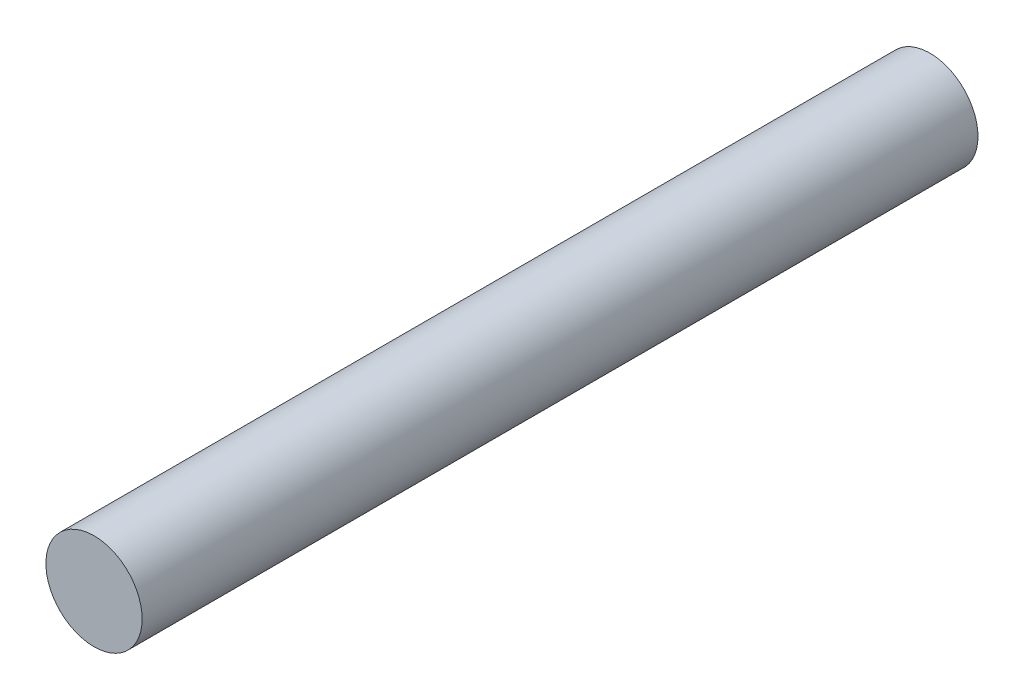
SolidWorks part; units mm, degrees
ref_plane "Front Plane" through (0, 0, 0) normal (0, 0, 1) x (1, 0, 0)
ref_plane "Top Plane" through (0, 0, 0) normal (0, 1, 0) x (1, 0, 0)
ref_plane "Right Plane" through (0, 0, 0) normal (1, 0, 0) x (0, 0, -1)
sketch "Sketch1" plane through (0, 0, 0) normal (0, 0, 1) x (1, 0, 0)
  circle A0 centre (0, 0) radius 4
extrude "Boss-Extrude1" add sketch "Sketch1" along normal blind 69.5
